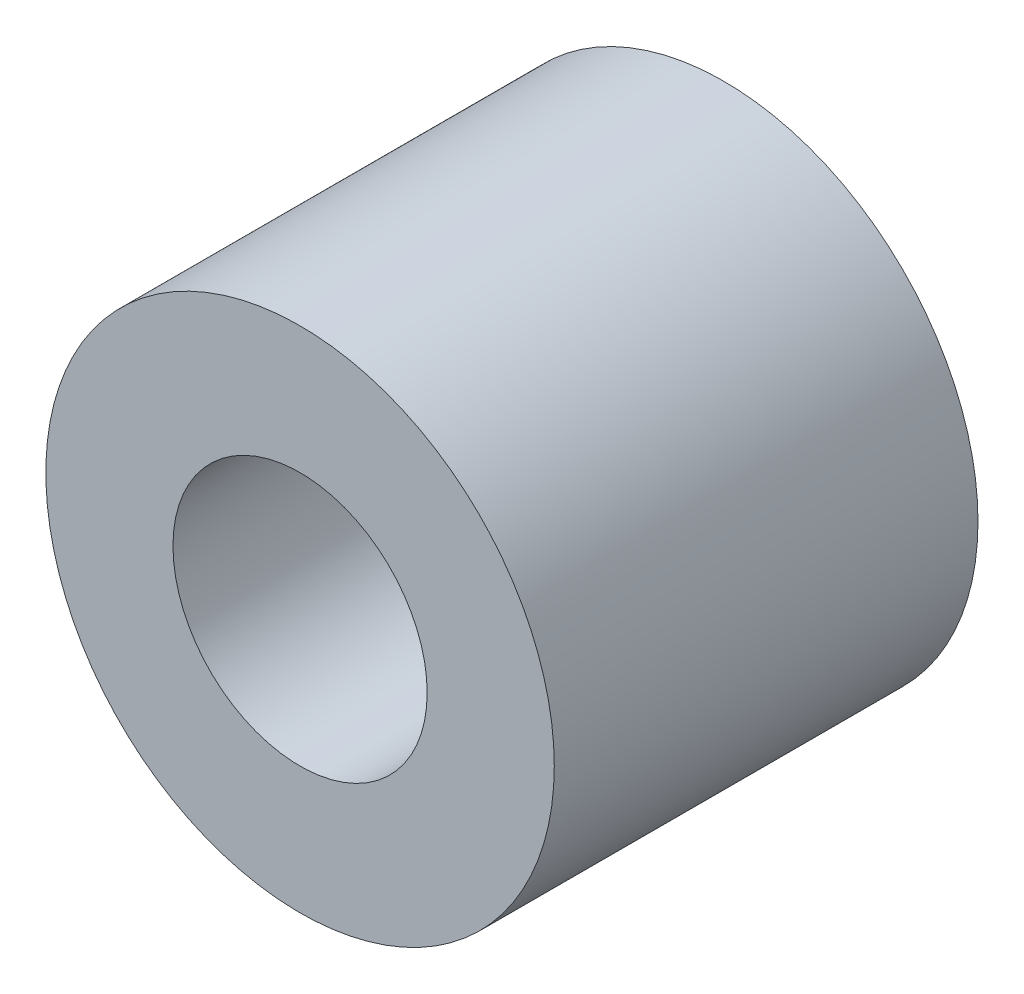
SolidWorks part; units mm, degrees
ref_plane "Front Plane" through (0, 0, 0) normal (0, 0, 1) x (1, 0, 0)
ref_plane "Top Plane" through (0, 0, 0) normal (0, 1, 0) x (1, 0, 0)
ref_plane "Right Plane" through (0, 0, 0) normal (1, 0, 0) x (0, 0, -1)
sketch "Sketch2" plane through (0, 0, 0) normal (0, 0, 1) x (1, 0, 0)
  circle A0 centre (0, 0) radius 1.5
  circle A1 centre (0, 0) radius 3
  dimension "D1" = 3
  dimension "D2" = 6
extrude "Boss-Extrude1" add sketch "Sketch2" along normal blind 5
